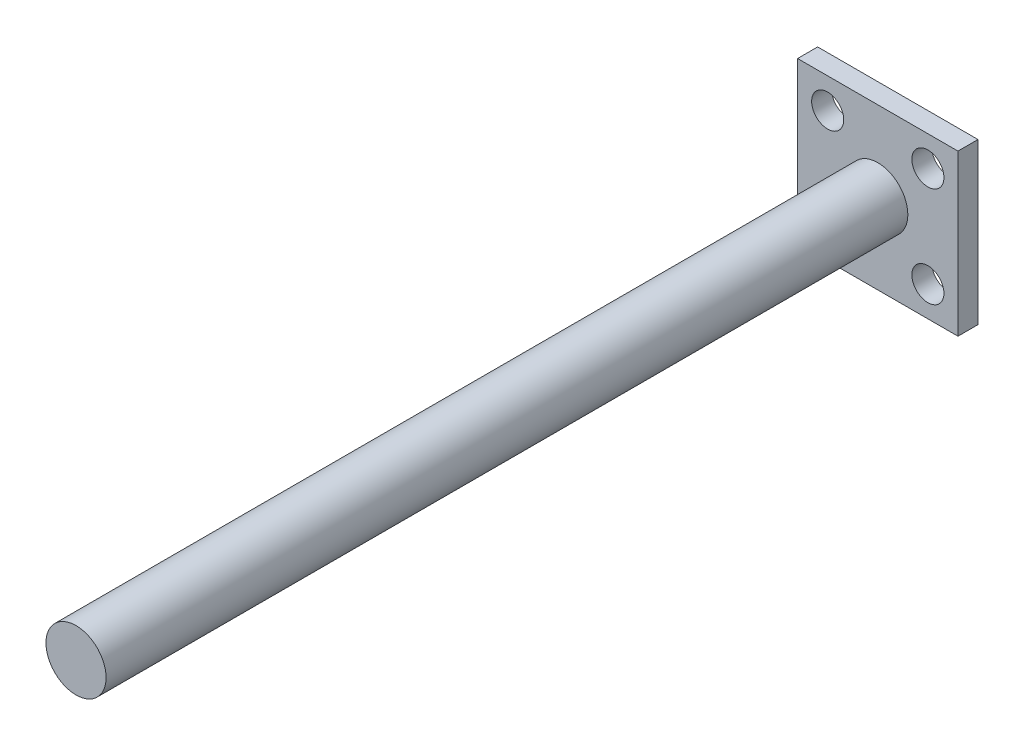
SolidWorks part; units mm, degrees
ref_plane "前视基准面" through (0, 0, 0) normal (0, 0, 1) x (1, 0, 0)
ref_plane "上视基准面" through (0, 0, 0) normal (0, 1, 0) x (1, 0, 0)
ref_plane "右视基准面" through (0, 0, 0) normal (1, 0, 0) x (0, 0, -1)
sketch "草图1" plane through (0, 0, 0) normal (0, 0, 1) x (1, 0, 0)
  line L1 (20, -20) -> (-20, -20)
  line L2 (20, -20) -> (20, 20)
  line L3 (20, 20) -> (-20, 20)
  line L4 (-20, -20) -> (-20, 20)
  line L5 (20, -20) -> (-20, 20) construction
  line L6 (20, 20) -> (-20, -20) construction
  line L7 (12.5, -12.5) -> (-12.5, -12.5) construction
  line L8 (12.5, -12.5) -> (12.5, 12.5) construction
  line L9 (12.5, 12.5) -> (-12.5, 12.5) construction
  line L10 (-12.5, -12.5) -> (-12.5, 12.5) construction
  line L11 (12.5, -12.5) -> (-12.5, 12.5) construction
  line L12 (12.5, 12.5) -> (-12.5, -12.5) construction
  circle A0 centre (-12.5, 12.5) radius 4
  circle A1 centre (12.5, 12.5) radius 4
  circle A2 centre (12.5, -12.5) radius 4
  circle A3 centre (-12.5, -12.5) radius 4
  point P0 (0, 0)
  point P6 (0, 0)
  dimension "D3" = 8
  dimension "D1" = 40
  dimension "D2" = 25
extrude "凸台-拉伸1" add sketch "草图1" along normal blind 5
sketch "草图2" plane through (0, 0, 5) normal (0, 0, 1) x (1, 0, 0)
  circle A0 centre (0, 0) radius 7.5
  dimension "D1" = 15
extrude "凸台-拉伸2" add sketch "草图2" along normal blind 200
